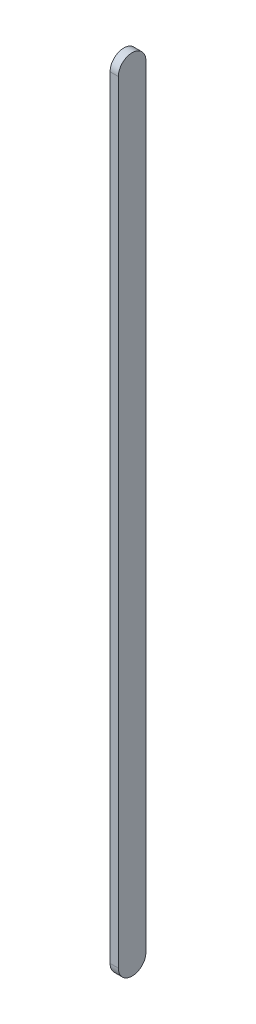
SolidWorks part; units mm, degrees
ref_plane "Front Plane" through (0, 0, 0) normal (0, 0, 1) x (1, 0, 0)
ref_plane "Top Plane" through (0, 0, 0) normal (0, 1, 0) x (1, 0, 0)
ref_plane "Right Plane" through (0, 0, 0) normal (1, 0, 0) x (0, 0, -1)
sketch "Sketch1" plane through (0, 0, 0) normal (1, 0, 0) x (0, 0, -1)
  line L0 (0, 0) -> (0, -280) construction
  line L1 (0, 0) -> (0, -280) construction
  line L2 (5, 0) -> (5, -280)
  line L3 (-5, 0) -> (-5, -280)
  arc A0 (5, 0) -> (-5, 0) centre (0, 0) ccw
  arc A1 (-5, -280) -> (5, -280) centre (0, -280) ccw
  point P3 (0, -140)
  dimension "D2" = 5
  dimension "D1" = 280
extrude "Boss-Extrude1" add sketch "Sketch1" along normal blind 3
